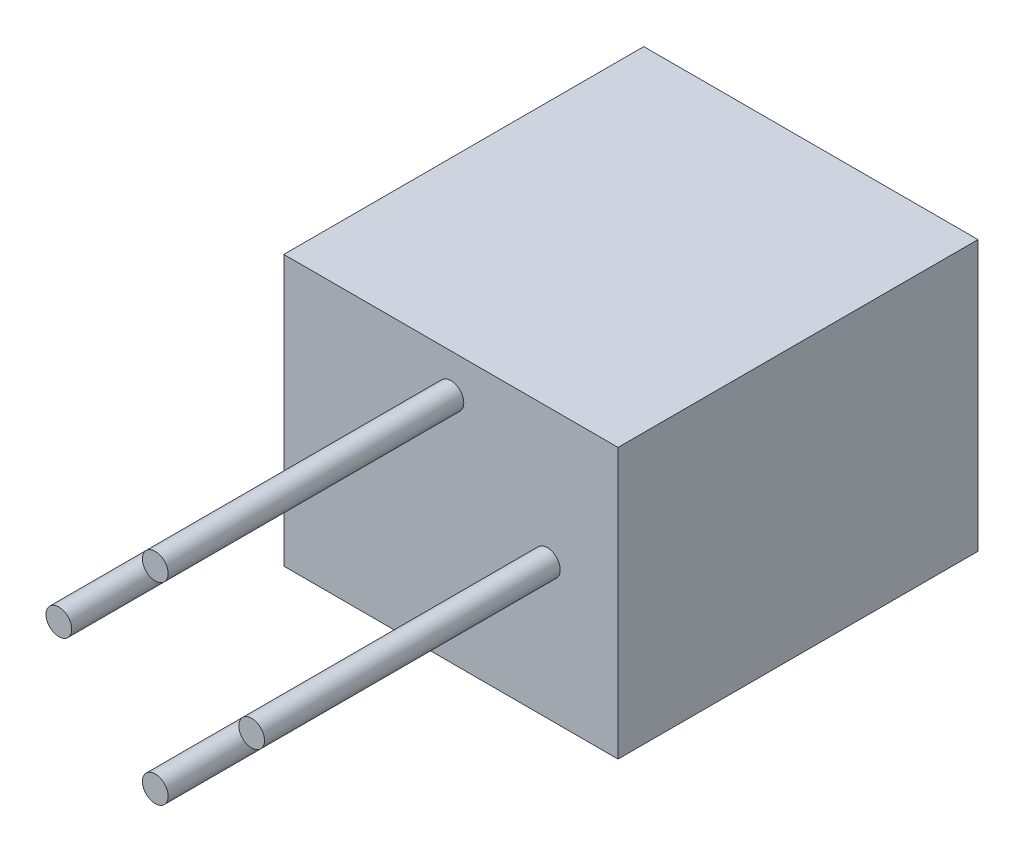
SolidWorks part; units mm, degrees
ref_plane "Front Plane" through (0, 0, 0) normal (0, 0, 1) x (1, 0, 0)
ref_plane "Top Plane" through (0, 0, 0) normal (0, 1, 0) x (1, 0, 0)
ref_plane "Right Plane" through (0, 0, 0) normal (1, 0, 0) x (0, 0, -1)
sketch "Sketch1" plane through (0, 0, 0) normal (0, 0, 1) x (1, 0, 0)
  line L0 (-8, -10.5) -> (18, -10.5)
  line L1 (18, -10.5) -> (18, 10.5)
  line L2 (18, 10.5) -> (-8, 10.5)
  line L3 (-8, 10.5) -> (-8, -10.5)
  line L4 (-5, -7.5) -> (15, -7.5)
  line L5 (15, -7.5) -> (15, 7.5)
  line L6 (15, 7.5) -> (-5, 7.5)
  line L7 (-5, 7.5) -> (-5, -7.5)
  line L8 (-5, -7.5) -> (15, -7.5)
  line L9 (15, -7.5) -> (15, 7.5)
  line L10 (15, 7.5) -> (-5, 7.5)
  line L11 (-5, 7.5) -> (-5, -7.5)
  dimension "D1" = 0
  dimension "D2" = 3
extrude "Boss-Extrude1" add sketch "Sketch1" against normal blind 25
sketch "Sketch2" plane through (0, 0, 0) normal (0, 0, 1) x (1, 0, 0)
  line L4 (-8, 10.5) -> (-8, -10.5)
  line L5 (-8, -10.5) -> (18, -10.5)
  line L6 (18, -10.5) -> (18, 10.5)
  line L7 (18, 10.5) -> (-8, 10.5)
  line L8 (-8, 10.5) -> (-8, -10.5)
  line L9 (-8, -10.5) -> (18, -10.5)
  line L10 (18, -10.5) -> (18, 10.5)
  line L11 (18, 10.5) -> (-8, 10.5)
  dimension "D1" = 0
extrude "Boss-Extrude2" add sketch "Sketch2" along normal blind 3
sketch "Sketch3" plane through (0, 0, 3) normal (0, 0, 1) x (1, 0, 0)
  line L0 (18, 10.5) -> (-8, -10.5) construction
  line L1 (-8, -10.5) -> (-8, 10.5) construction
  line L2 (-8, 10.5) -> (18, -10.5) construction
  circle A0 centre (5, 0) radius 7.5 construction
  circle A1 centre (12.5, 0) radius 1
  circle A2 centre (5, -7.5) radius 1
  circle A3 centre (-2.5, 0) radius 1
  circle A4 centre (5, 7.5) radius 1
  point P21 (5, 0)
  dimension "D1" = 15
  dimension "D2" = 2
  dimension "D3" = 4
extrude "Boss-Extrude3" add sketch "Sketch3" along normal blind 23
